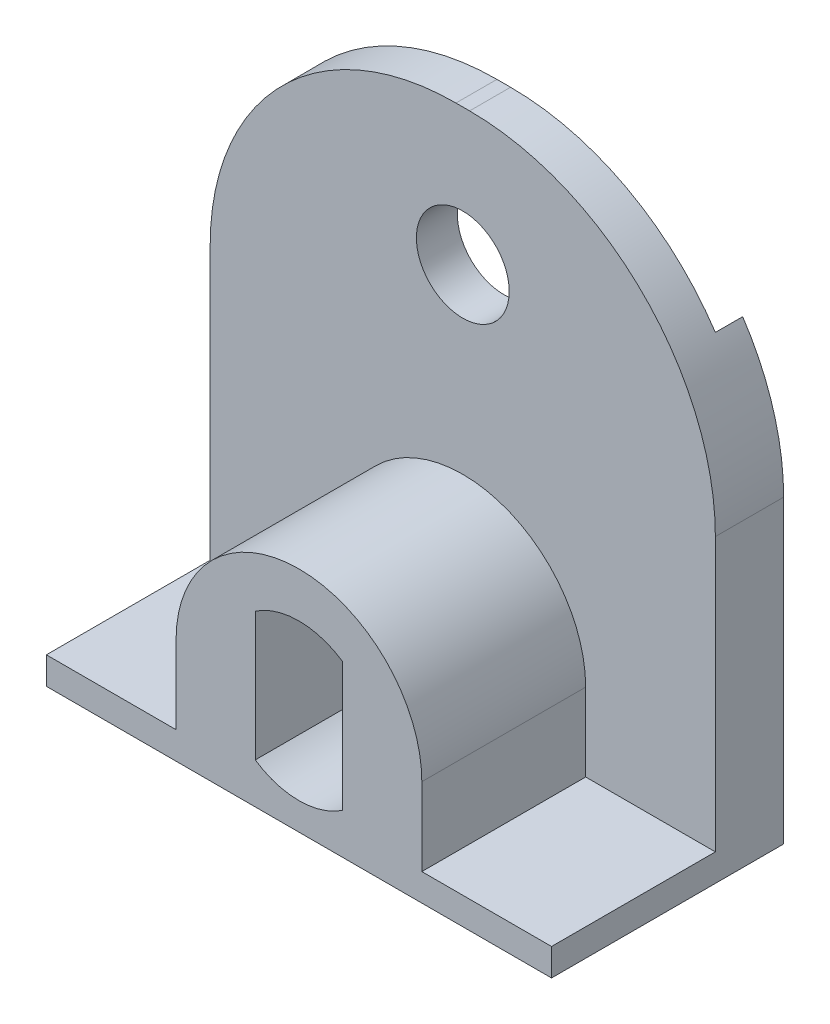
SolidWorks part; units mm, degrees
ref_plane "Спереди" through (0, 0, 0) normal (0, 0, 1) x (1, 0, 0)
ref_plane "Сверху" through (0, 0, 0) normal (0, 1, 0) x (1, 0, 0)
ref_plane "Справа" through (0, 0, 0) normal (1, 0, 0) x (0, 0, -1)
sketch "Эскиз1" plane through (0, 0, 0) normal (0, 1, 0) x (1, 0, 0)
  line L0 (0, 0) -> (15.5, 0)
  line L1 (0, 0) -> (0, 1)
  line L2 (0, 1) -> (-1.5, 1)
  line L3 (-1.5, 1) -> (-1.5, -1.5)
  line L4 (-1.5, -1.5) -> (17, -1.5)
  line L5 (17, -1.5) -> (17, 1)
  line L6 (17, 1) -> (15.5, 1)
  line L7 (15.5, 1) -> (15.5, 0)
  dimension "D1" = 15.5
  dimension "D2" = 1.5
  dimension "D3" = 1.5
  dimension "D4" = 1
  dimension "D5" = 1
  dimension "D6" = 2.5
extrude "Бобышка-Вытянуть1" add sketch "Эскиз1" along normal blind 20
fillet "Скругление1" radius 9 2 edges at (-1.5, 20, 0.25) (17, 20, 0.25)
sketch "Эскиз2" plane through (0, 0, 1.5) normal (0, 0, 1) x (1, 0, 0)
  line L0 (7.5, 20) -> (8, 20) construction
  circle A0 centre (7.75, 15) radius 1.7
  point P2 (0, 0)
  point P5 (0, 0)
  point P6 (7.75, 20)
  dimension "D1" = 3.4
  dimension "D2" = 5
extrude "Вырез-Вытянуть1" cut sketch "Эскиз2" against normal through all
sketch "Эскиз3" plane through (0, 0, 1.5) normal (0, 0, 1) x (1, 0, 0)
  line L0 (17, 11) -> (17, 0) construction
  line L1 (-1.5, 0) -> (17, 0)
  line L2 (-1.5, 0) -> (-1.5, 1)
  line L3 (-1.5, 1) -> (17, 1)
  line L4 (17, 0) -> (17, 1)
  point P7 (7.75, 1)
  point P8 (7.75, 0)
  dimension "D1" = 1
extrude "Бобышка-Вытянуть2" add sketch "Эскиз3" along normal blind 6
sketch "Эскиз4" plane through (0, 0, 1.5) normal (0, 0, 1) x (1, 0, 0)
  line L0 (17, 1) -> (-1.5, 1) construction
  line L1 (6.15, 6.2085) -> (6.15, 1.4915)
  line L2 (9.35, 6.2085) -> (9.35, 1.4915)
  line L3 (3.25, 3.85) -> (3.25, 1.0238)
  line L4 (3.25, 1.0238) -> (3.25, 0.7754)
  line L5 (12.25, 1.0238) -> (12.25, 3.85)
  line L6 (3.25, 0.7754) -> (12.25, 0.7754)
  line L7 (12.25, 0.7754) -> (12.25, 1.0238)
  arc A0 (6.15, 1.4915) -> (9.35, 1.4915) centre (7.75, 3.85) ccw
  arc A1 (9.35, 6.2085) -> (6.15, 6.2085) centre (7.75, 3.85) ccw
  arc A2 (12.25, 3.85) -> (3.25, 3.85) centre (7.75, 3.85) ccw
  point P1 (9.35, 3.85)
  point P4 (7.75, 1)
  point P7 (6.15, 3.85)
  dimension "D1" = 5.7
  dimension "D3" = 9
  dimension "D2" = 1.6
  dimension "D4" = 1.6
extrude "Бобышка-Вытянуть3" add sketch "Эскиз4" along normal up to surface (6 mm away) up to face at (7.75, 0.5, 7.5)
